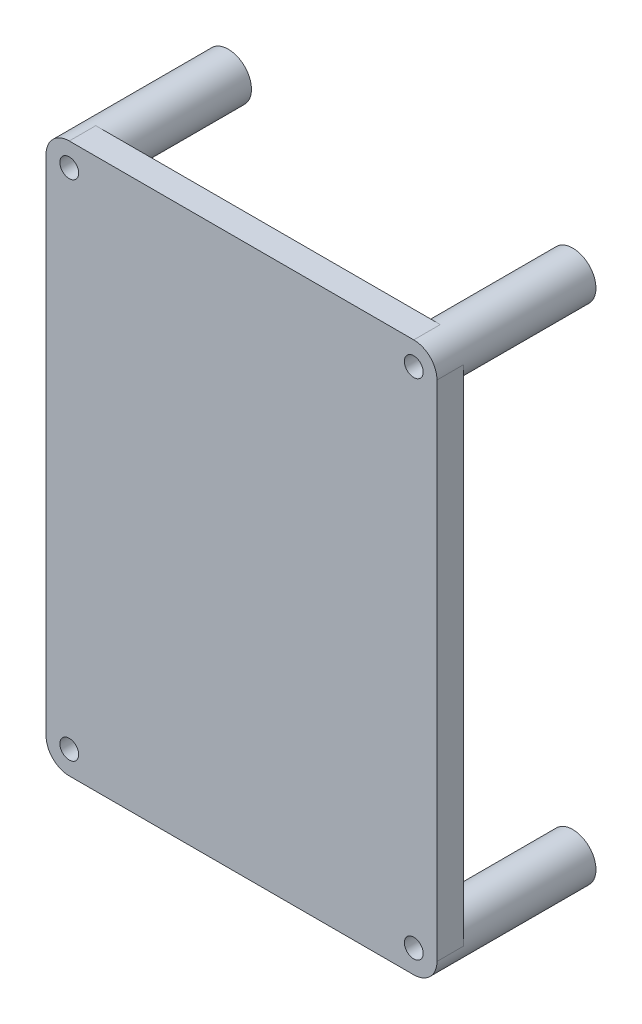
SolidWorks part; units mm, degrees
ref_plane "Front Plane" through (0, 0, 0) normal (0, 0, 1) x (1, 0, 0)
ref_plane "Top Plane" through (0, 0, 0) normal (0, 1, 0) x (1, 0, 0)
ref_plane "Right Plane" through (0, 0, 0) normal (1, 0, 0) x (0, 0, -1)
sketch "Sketch1" plane through (0, 0, 206.2667) normal (0, 0, 1) x (1, 0, 0)
  line L0 (164.0266, 113.2302) -> (164.0266, 189.2302) construction
  line L1 (108.5266, 109.7302) -> (160.5266, 109.7302) construction
  line L2 (105.0266, 189.2302) -> (105.0266, 113.2302) construction
  line L3 (160.5266, 192.7302) -> (108.5266, 192.7302) construction
  line L4 (164.0266, 113.2302) -> (164.0266, 189.2302)
  line L5 (108.5266, 109.7302) -> (160.5266, 109.7302)
  line L6 (105.0266, 189.2302) -> (105.0266, 113.2302)
  line L7 (160.5266, 192.7302) -> (108.5266, 192.7302)
  circle A0 centre (108.5266, 189.2302) radius 3.5 construction
  circle A1 centre (160.5266, 189.2302) radius 3.5 construction
  circle A2 centre (160.5266, 113.2302) radius 3.5 construction
  circle A3 centre (108.5266, 113.2302) radius 3.5 construction
  arc A4 (108.5266, 192.7302) -> (105.0266, 189.2302) centre (108.5266, 189.2302) ccw
  arc A5 (164.0266, 189.2302) -> (160.5266, 192.7302) centre (160.5266, 189.2302) ccw
  arc A6 (160.5266, 109.7302) -> (164.0266, 113.2302) centre (160.5266, 113.2302) ccw
  arc A7 (105.0266, 113.2302) -> (108.5266, 109.7302) centre (108.5266, 113.2302) ccw
  circle A8 centre (160.5266, 113.2302) radius 1.4224 construction
  circle A9 centre (108.5266, 113.2302) radius 1.4224 construction
  circle A10 centre (160.5266, 189.2302) radius 1.4224 construction
  circle A11 centre (108.5266, 189.2302) radius 1.4224 construction
  circle A12 centre (160.5266, 113.2302) radius 1.4224
  circle A13 centre (108.5266, 113.2302) radius 1.4224
  circle A14 centre (160.5266, 189.2302) radius 1.4224
  circle A15 centre (108.5266, 189.2302) radius 1.4224
extrude "Boss-Extrude1" add sketch "Sketch1" along normal blind 4
sketch "Sketch3" plane through (0, 0, 206.2667) normal (0, 0, -1) x (-1, 0, 0)
  circle A0 centre (-108.5266, 189.2302) radius 1.4224
  circle A1 centre (-108.5266, 189.2302) radius 3.5
  circle A2 centre (-160.5266, 189.2302) radius 1.4224
  circle A3 centre (-160.5266, 189.2302) radius 3.5
  circle A4 centre (-160.5266, 113.2302) radius 1.4224
  circle A5 centre (-160.5266, 113.2302) radius 3.5
  circle A6 centre (-108.5266, 113.2302) radius 1.4224
  circle A7 centre (-108.5266, 113.2302) radius 3.5
extrude "Boss-Extrude2" add sketch "Sketch3" along normal blind 20
